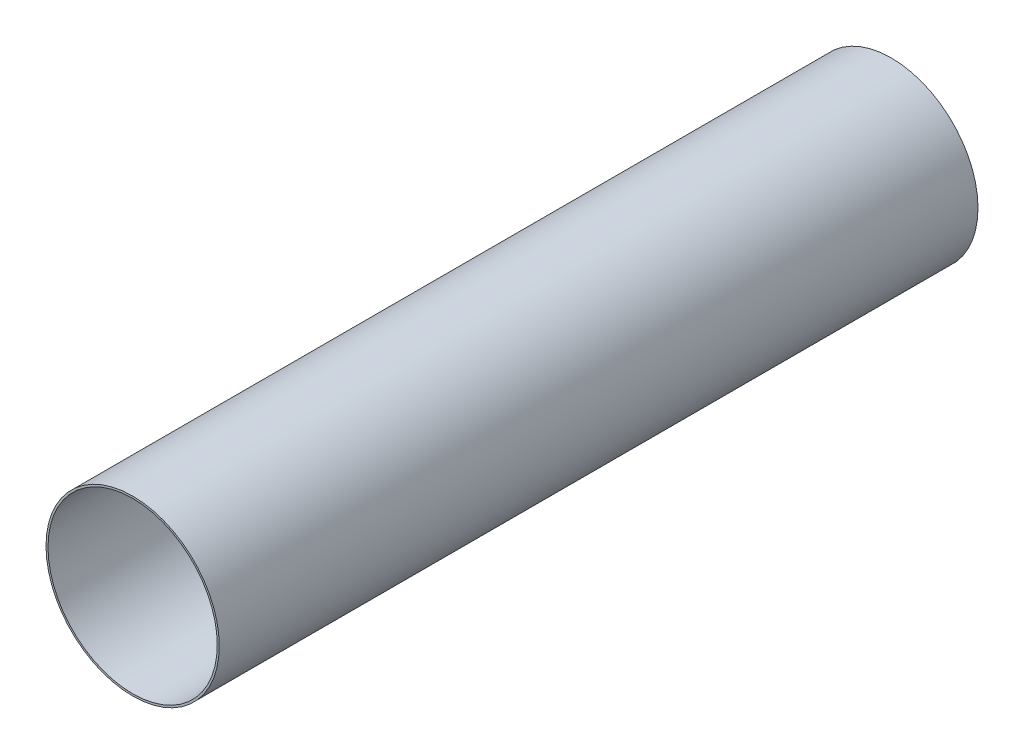
SolidWorks part; units mm, degrees
material "Thornel Mat VMA"
ref_plane "Front Plane" through (0, 0, 0) normal (0, 0, 1) x (1, 0, 0)
ref_plane "Top Plane" through (0, 0, 0) normal (0, 1, 0) x (1, 0, 0)
ref_plane "Right Plane" through (0, 0, 0) normal (1, 0, 0) x (0, 0, -1)
sketch "Sketch1" plane through (0, 0, 0) normal (0, 0, 1) x (1, 0, 0)
  circle A0 centre (0, 0) radius 86.9998
  circle A1 centre (0, 0) radius 84.9998
  dimension "D1" = 169.9997
  dimension "D2" = 173.9997
extrude "Boss-Extrude1" add sketch "Sketch1" along normal mid plane 762
equation "\"TubeDiameter\" = 6.6929in"
equation "\"D1@Sketch1\"=\"TubeDiameter\""
equation "\"D2@Sketch1\"=\"TubeDiameter\"+4mm"
